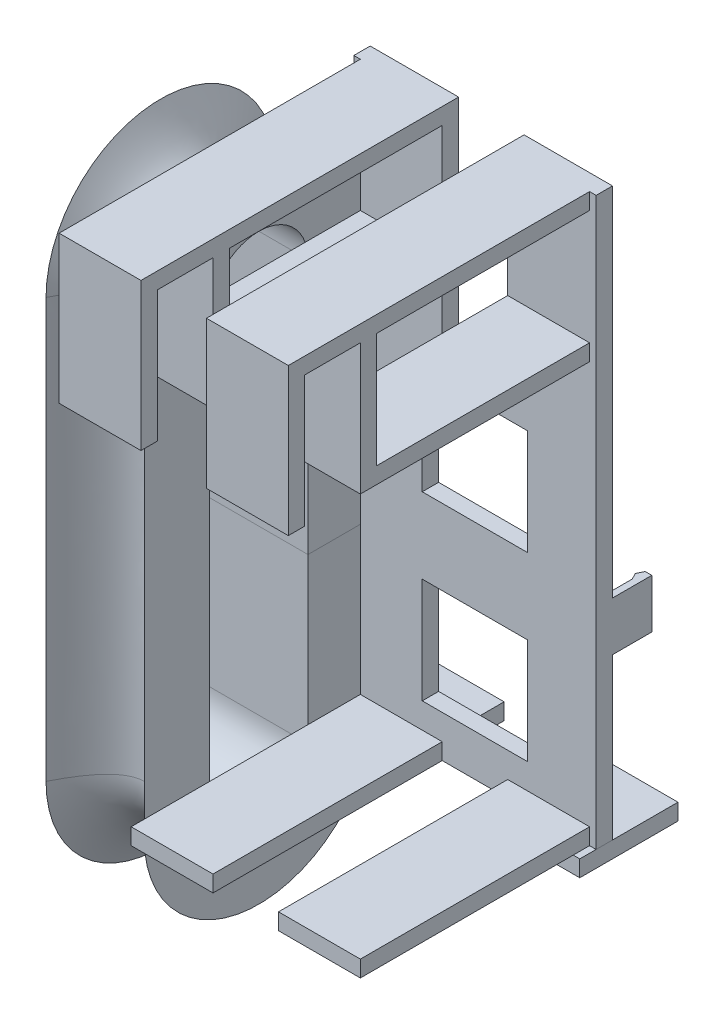
SolidWorks part; units mm, degrees
ref_plane "Front Plane" through (0, 0, 0) normal (0, 0, 1) x (1, 0, 0)
ref_plane "Top Plane" through (0, 0, 0) normal (0, 1, 0) x (1, 0, 0)
ref_plane "Right Plane" through (0, 0, 0) normal (1, 0, 0) x (0, 0, -1)
sketch "Sketch1" plane through (0, 0, 0) normal (0, 0, 1) x (1, 0, 0)
  line L0 (35, 87.5) -> (35, 113) construction
  line L1 (0, 0) -> (70, 0)
  line L2 (0, 0) -> (0, 113)
  line L3 (0, 113) -> (70, 113)
  line L4 (70, 0) -> (70, 113)
  line L5 (0, 113) -> (25, 113)
  line L6 (0, 113) -> (0, 173)
  line L7 (0, 173) -> (25, 173)
  line L8 (25, 113) -> (25, 173)
  line L9 (70, 113) -> (45, 113)
  line L10 (70, 113) -> (70, 173)
  line L11 (70, 173) -> (45, 173)
  line L12 (45, 113) -> (45, 173)
  line L13 (0, 56.5) -> (70, 56.5) construction
  line L14 (18.9, 68.05) -> (51.1, 68.05)
  line L15 (18.9, 68.05) -> (18.9, 100.25)
  line L16 (18.9, 100.25) -> (51.1, 100.25)
  line L17 (51.1, 68.05) -> (51.1, 100.25)
  line L18 (18.9, 12.75) -> (51.1, 12.75)
  line L19 (51.1, 44.95) -> (51.1, 12.75)
  line L20 (18.9, 44.95) -> (51.1, 44.95)
  line L21 (18.9, 44.95) -> (18.9, 12.75)
  line L23 (0, 173) -> (-2, 173)
  line L24 (0, 173) -> (0, 0)
  line L25 (0, 0) -> (-2, 0)
  line L26 (-2, 173) -> (-2, 0)
  line L27 (70, 0) -> (72, 0)
  line L28 (70, 0) -> (70, 173)
  line L29 (70, 173) -> (72, 173)
  line L30 (72, 0) -> (72, 173)
  point P11 (35, 87.5)
  point P21 (35, 100.25)
  dimension "D1" = 70
  dimension "D2" = 113
  dimension "D3" = 60
  dimension "D4" = 25.5
  dimension "D5" = 32.2
  dimension "D6" = 25
  dimension "D7" = 2
extrude "Boss-Extrude1" add sketch "Sketch1" along normal blind 5 contours L3 L8 L7 L6 | L12 L3 L10 L11 | L1 L4 L3 L2 L21 L20 L19 L18 L17 L14 L15 L16 | L23 L26 L25 L2 L6 | L27 L30 L29 L10 L4
sketch "Sketch2" plane through (0, 0, 0) normal (1, 0, 0) x (0, 0, -1)
  line L1 (-5, 173) -> (-97, 173)
  line L2 (-5, 173) -> (-5, 168)
  line L3 (-5, 168) -> (-97, 168)
  line L4 (-97, 173) -> (-97, 168)
  line L5 (-97, 168) -> (-92, 168)
  line L6 (-97, 168) -> (-97, 128)
  line L7 (-97, 128) -> (-92, 128)
  line L8 (-92, 168) -> (-92, 128)
  line L10 (-75, 168) -> (-70, 168)
  line L11 (-75, 168) -> (-75, 128)
  line L12 (-75, 128) -> (-70, 128)
  line L13 (-70, 168) -> (-70, 128)
  line L14 (-5, 173) -> (-5, 0) construction
  line L15 (-70, 128) -> (-5, 128)
  line L16 (-70, 128) -> (-70, 133)
  line L17 (-70, 133) -> (-5, 133)
  line L18 (-5, 128) -> (-5, 133)
  line L19 (-5, 0) -> (-75, 0)
  line L20 (-5, 0) -> (-5, 5)
  line L21 (-5, 5) -> (-75, 5)
  line L22 (-75, 0) -> (-75, 5)
  dimension "D1" = 5
  dimension "D2" = 40
  dimension "D3" = 17
  dimension "D5" = 5
  dimension "D4" = 70
extrude "Boss-Extrude2" add sketch "Sketch2" along normal blind 25 contours L15 L18 L17 L13 | L13 L3 L11 L12 | L8 L3 L6 L7 | L1 L4 L3 L2 | L22 L19 L20 L21
ref_plane "Mid Pane" through (35, 0, 0) normal (1, 0, 0) x (0, 0, -1)
mirror "Mirror2" about plane through (35, 0, 0) normal (1, 0, 0) of "Boss-Extrude2"
sketch "Sketch3" plane through (0, 0, 0) normal (1, 0, 0) x (0, 0, -1)
  line L0 (0, 64) -> (0, 49)
  line L1 (0, 0) -> (0, 173) construction
  line L2 (-5, 0) -> (0, 0) construction
  line L3 (0, 49) -> (12, 49)
  line L4 (12, 49) -> (12, 64)
  line L5 (12, 64) -> (0, 64)
  point P5 (0, 56.5)
  point P8 (-2.5, 0)
  dimension "D1" = 56.5
  dimension "D2" = 15
  dimension "D3" = 12
extrude "Boss-Extrude3" add sketch "Sketch3" against normal through all
sketch "Sketch4" plane through (0, 64, 0) normal (0, 1, 0) x (1, 0, 0)
  line L0 (0, 12) -> (1, 10)
  line L1 (1, 10) -> (0, 10)
  line L2 (0, 12) -> (0, 0) construction
  line L3 (0, 8) -> (0, 12)
  line L4 (0, 8) -> (1, 10)
  line M7 (0, 0) -> (0, 12)
  dimension "D1" = 2
  dimension "D2" = 1
extrude "Boss-Extrude5" add sketch "Sketch4" against normal up to surface (15 mm away) contours L1 L0 M7 | L4 L1 M7 up to face at (-1, 49, -6)
mirror "Mirror3" about plane through (35, 0, 0) normal (1, 0, 0) of "Boss-Extrude5", "Boss-Extrude3"
sketch "Sketch5" plane through (0, 0, 0) normal (0, 0, -1) x (-1, 0, 0)
  line L0 (-72, 0) -> (2, 0) construction
  line L1 (-72, 0) -> (-51.1, 0)
  line L2 (-72, 0) -> (-72, -5)
  line L3 (-72, -5) -> (-51.1, -5)
  line L4 (-51.1, 0) -> (-51.1, -5)
  line L7 (-72, 0) -> (-72, 49) construction
  line L8 (-51.1, 44.95) -> (-51.1, 12.75) construction
  line L9 (-18.9, 0) -> (2, 0)
  line L10 (-18.9, 0) -> (-18.9, -5)
  line L11 (-18.9, -5) -> (2, -5)
  line L12 (2, 0) -> (2, -5)
  line L13 (-18.9, 44.95) -> (-18.9, 12.75) construction
  dimension "D1" = 5
extrude "Boss-Extrude6" add sketch "Sketch5" along normal blind 20 and the other way blind 10 separate body
fillet "Fillet1" radius 2 2 edges at (0, 56.5, 0) (70, 56.5, 0)
sketch "Sketch7" plane through (0, 0, 0) normal (-1, 0, 0) x (0, 0, 1)
  line L0 (36, 128) -> (36, 0) construction
  line L1 (51, 128) -> (51, 0)
  line L2 (21, 128) -> (21, 0)
  line L7 (5, 173) -> (5, 0) construction
  line L9 (75, 128) -> (5, 128) construction
  line L10 (5, 0) -> (75, 0) construction
  arc A0 (51, 128) -> (21, 128) centre (36, 128) ccw
  arc A1 (21, 0) -> (51, 0) centre (36, 0) ccw
  point P2 (36, 64)
  point P7 (0, 0)
  point P9 (0, 0)
  point P15 (0, 0)
  dimension "D1" = 30
  dimension "D2" = 16
ref_plane "Plane2" through (0, 50, 0) normal (0, 1, 0) x (1, 0, 0)
sketch "Sketch8" plane through (0, 50, 0) normal (0, 1, 0) x (1, 0, 0)
  line L0 (0, -21) -> (-30, -21)
  line L1 (0, -21) -> (0, -1)
  line L2 (-30, -21) -> (-30, -1)
  line L3 (-15, -21) -> (-15, -16) construction
  spline S0 degree 2 poles (-30, -1) (-15, -31) (0, -1) knots 0 0 0 1 1 1
  dimension "D1" = 30
  dimension "D2" = 5
  dimension "D3" = 20
sweep "Sweep5" add profiles "Sketch8" path "Sketch7"
equation "\"plateThickness\"=0.005"
equation "\"D1@Boss-Extrude1\"=\"plateThickness\""
equation "\"D1@Sketch2\"=\"plateThickness\""
equation "\"D5@Sketch2\"=\"plateThickness\""
equation "\"D1@Sketch5\"=\"plateThickness\""
equation "\"D2@Boss-Extrude6\"=\"plateThickness\""
